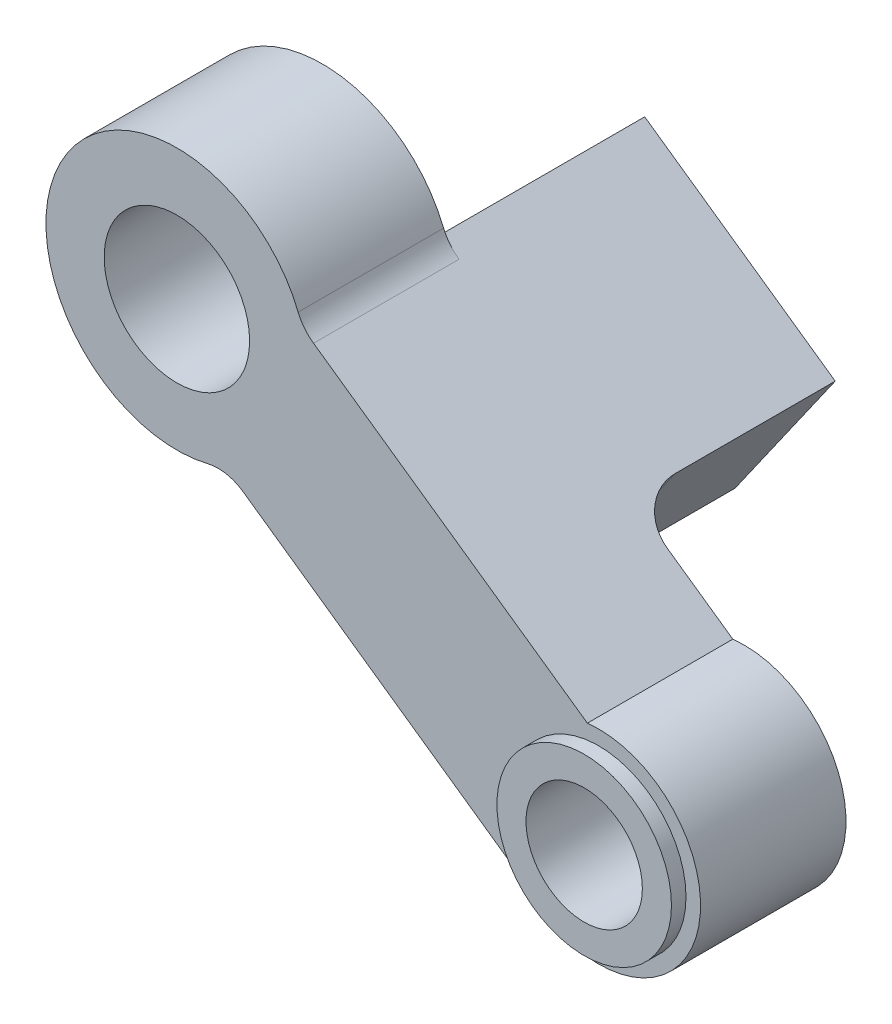
SolidWorks part; units mm, degrees
ref_plane "前视基准面" through (0, 0, 0) normal (0, 0, 1) x (1, 0, 0)
ref_plane "上视基准面" through (0, 0, 0) normal (0, 1, 0) x (1, 0, 0)
ref_plane "右视基准面" through (0, 0, 0) normal (1, 0, 0) x (0, 0, -1)
sketch "草图1" plane through (0, 0, 0) normal (0, 0, 1) x (1, 0, 0)
  line L0 (0, 0) -> (-7.5, 12.9904)
  line L2 (0, 0) -> (10, 0) construction
  dimension "D1" = 60
  dimension "D2" = 15
sketch "草图4" plane through (0, 0, 0) normal (0, 0, 1) x (1, 0, 0)
  line L0 (1.682, -1.8495) -> (2.1208, -1.3237) construction
  line L1 (4.3067, 1.3047) -> (14.1097, -5.5718)
  line L2 (0, 0) -> (0, 30) construction
  line L3 (0, 30) -> (11.5, 17.3547) construction
  line L4 (1.5803, -1.9372) -> (2.0467, -1.4357) construction
  line L5 (0, 0) -> (2.0467, -1.4357) construction
  line L6 (-31.7674, -4.8074) -> (16, -4.8074) construction
  line L7 (0, 0) -> (1.5803, -1.9372) construction
  line L8 (0, 0) -> (14.5, -9.05) construction
  line L9 (0, 0) -> (11.5, -12.6453) construction
  line L10 (16, -4.8074) -> (16, -32.0113) construction
  line L11 (11.8071, -11.2856) -> (-1.7827, -1.7527) construction
  line L12 (16, -4.8074) -> (16, 17.3547) construction
  line L13 (1.6736, -4.1772) -> (11.8071, -11.2856)
  line L14 (0, -8.5) -> (0, -19.5) construction
  line L15 (0, -19.5) -> (-1.9101, -8.6671) construction
  line L16 (-2.1914, -1.2032) -> (8.3014, -14.0662) construction
  line L17 (1.5803, -1.9372) -> (-0.3249, -3.4913) construction
  line L18 (11.5, -4.8074) -> (0, -17.4526) construction
  line L19 (2.0467, -1.4357) -> (0.6347, -3.4485) construction
  circle A0 centre (14.5, -9.05) radius 2
  arc A1 (11.8071, -11.2856) -> (14.1097, -5.5718) centre (14.5, -9.05) ccw
  circle A2 centre (14.5, -9.05) radius 4.5 construction
  circle A3 centre (11.5, -12.6453) radius 4.5 construction
  circle A4 centre (11.5, 17.3547) radius 4.5 construction
  circle A5 centre (0, -8.5) radius 4.5 construction
  circle A6 centre (-1.9101, -8.6671) radius 4.5 construction
  circle A7 centre (11.5, -4.8074) radius 4.5 construction
  circle A8 centre (0, 0) radius 2.5
  arc A9 (1.6736, -4.1772) -> (4.3067, 1.3047) centre (0, 0) cw
  point P1 (2.1208, -1.3237)
  point P28 (1.682, -1.8495)
  point P36 (0, 0)
  dimension "D3" = 4
  dimension "D4" = 3.5
  dimension "D5" = 9
  dimension "D6" = 19.5
  dimension "D7" = 9
  dimension "D9" = 11
  dimension "D11" = 3
  dimension "D8" = 5
  dimension "D14" = 4.5
  dimension "D16" = 30
  dimension "D17" = 17.4526
  dimension "D2" = 16
  dimension "D10" = 10
  dimension "D12" = 10.45
  dimension "D13" = 14.6926
  dimension "D15" = 6
extrude "凸台-拉伸1" add sketch "草图4" along normal blind 5
sketch "草图5" plane through (0, 0, 0) normal (0, 0, -1) x (-1, 0, 0)
  line L0 (-1.6736, -4.1772) -> (-11.8071, -11.2856) construction
  line L1 (-0.6347, -3.4485) -> (-7.184, -8.0427)
  line L2 (-0.6347, -3.4485) -> (-4.0804, 1.4635)
  line L3 (-7.184, -8.0427) -> (-10.6297, -3.1307)
  line L5 (-4.0804, 1.4635) -> (-10.6297, -3.1307)
  line L6 (-14.1097, -5.5718) -> (-4.3067, 1.3047) construction
  circle A0 centre (0, 0) radius 2.5 construction
  dimension "D1" = 8
extrude "凸台-拉伸2" add sketch "草图5" along normal blind 7 and the other way up to surface (5 mm away) other way up to face at (2.5, 0, 5)
fillet "圆角3" radius 1.5 2 edges at (4.3067, 1.3047, 2.5) (8.9069, -5.5867, 0)
fillet "圆角4" radius 1.5 2 edges at (1.6736, -4.1772, 2.5) (11.8071, -11.2856, 2.5)
sketch "草图6" plane through (0, 0, 5) normal (0, 0, 1) x (1, 0, 0)
  circle A0 centre (14.5, -9.05) radius 2 construction
  circle A1 centre (14.5, -9.05) radius 2
  circle A2 centre (14.5, -9.05) radius 3
  dimension "D1" = 1
extrude "凸台-拉伸3" add sketch "草图6" along normal blind 0.5
